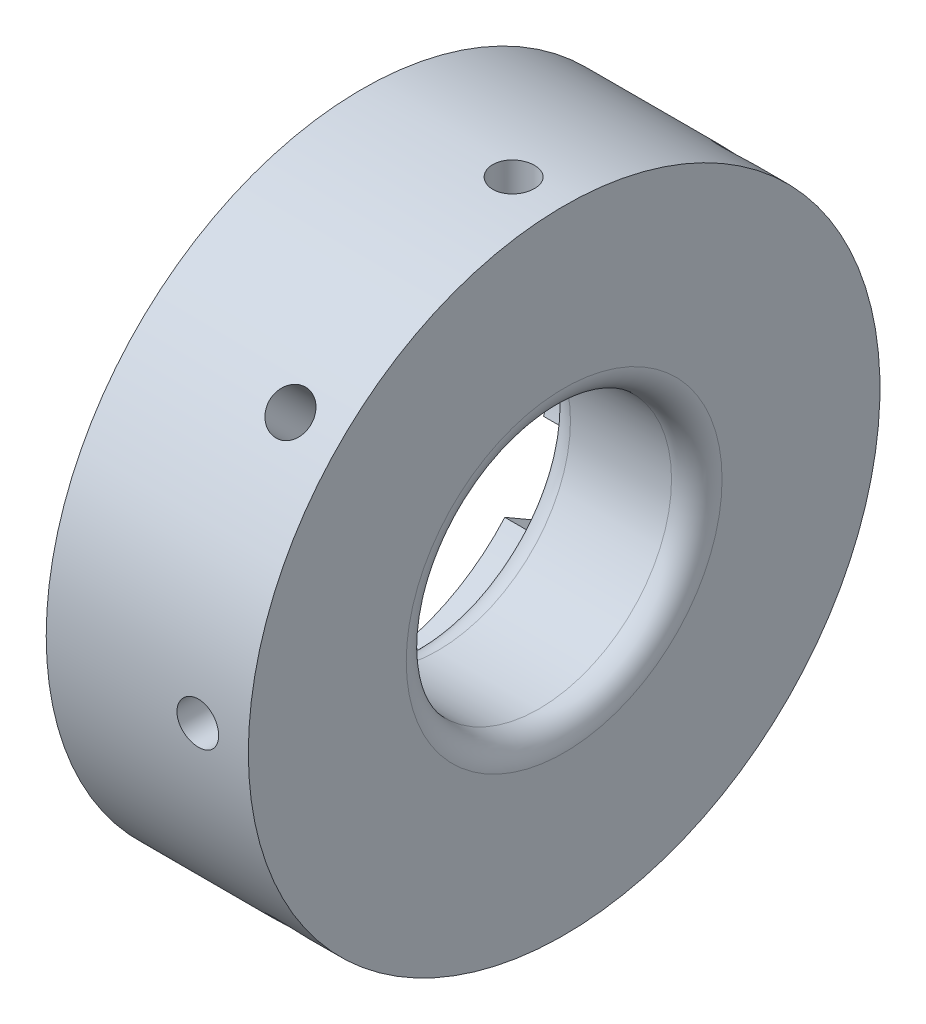
SolidWorks part; units mm, degrees
ref_plane "Plan de face" through (0, 0, 0) normal (0, 0, 1) x (1, 0, 0)
ref_plane "Plan de dessus" through (0, 0, 0) normal (0, 1, 0) x (1, 0, 0)
ref_plane "Plan de droite" through (0, 0, 0) normal (1, 0, 0) x (0, 0, -1)
sketch "Esquisse1" plane through (0, 0, 0) normal (0, 0, 1) x (1, 0, 0)
  line L0 (0, 0) -> (182.6544, 0) construction
  line L2 (0, 25) -> (16, 25)
  line L5 (16, 25) -> (16, 10.5)
  line L9 (0, 25) -> (0, 10.5)
  line L10 (0, 10.5) -> (16, 10.5)
  dimension "D1" = 25
  dimension "D2" = 21
  dimension "D4" = 16
revolve "Révolution1" add sketch "Esquisse1" angle 360 about L0
sketch "Esquisse2" plane through (0, 0, 0) normal (-1, 0, 0) x (0, 0, 1)
  line L0 (-3.02, 18.9998) -> (-3.02, 14.7949)
  line L1 (3.18, 18.9998) -> (3.18, 14.7614)
  line L2 (18.0443, 6.746) -> (14.3737, 4.6267)
  line L3 (14.9443, 12.1153) -> (11.3028, 10.0129)
  line L4 (14.8643, -12.2539) -> (11.1937, -10.1346)
  line L5 (17.9643, -6.8845) -> (14.3228, -4.7821)
  line L6 (-3.18, -18.9998) -> (-3.18, -14.7614)
  line L7 (3.02, -18.9998) -> (3.02, -14.7949)
  line L8 (-18.0443, -6.746) -> (-14.3737, -4.6267)
  line L9 (-14.9443, -12.1153) -> (-11.3028, -10.0129)
  line L10 (-14.8643, 12.2539) -> (-11.1937, 10.1346)
  line L11 (-17.9643, 6.8845) -> (-14.3228, 4.7821)
  circle A0 centre (0, 0) radius 15.1
  circle A1 centre (0, 0) radius 4.1
  circle A2 centre (0.08, 18.9998) radius 3.1
  circle A3 centre (16.4943, 9.4306) radius 3.1
  circle A4 centre (16.4143, -9.5692) radius 3.1
  circle A5 centre (-0.08, -18.9998) radius 3.1
  circle A6 centre (-16.4943, -9.4306) radius 3.1
  circle A7 centre (-16.4143, 9.5692) radius 3.1
  point P43 (0, 0)
  dimension "D1" = 8.2
  dimension "D2" = 30.2
  dimension "D3" = 6.2
  dimension "D6" = 6.2
  dimension "D4" = 19
  dimension "D5" = 6
extrude "Enlèv. mat.-Extru.1" cut sketch "Esquisse2" against normal blind 4 contours A0 A1 | A7 | A7 L11 A0 L10 | A6 | A6 L9 A0 L8 | A5 L7 A0 L6 | A4 L5 A0 L4 | A3 L3 A0 L2 | A3 | A4 | A2 | A2 L0 A0 L1
fillet "Congé2" radius 2 1 edges at (4, 0, 10.5)
fillet "Congé3" radius 2 1 edges at (16, 0, 10.5)
sketch "Esquisse3" plane through (0, 0, 0) normal (0, 0, 1) x (1, 0, 0)
  line L0 (0, 0) -> (16, 0) construction
  line L1 (16, -25) -> (16, 25) construction
  circle A0 centre (12, 0) radius 1.65
  dimension "D2" = 3.3
  dimension "D1" = 4
extrude "Enlèv. mat.-Extru.2" cut sketch "Esquisse3" against normal blind 10 from offset 25
pattern_circular "Répétition circulaire1" count 8 over 360 about axis through (0, 0, 0) along (1, 0, 0) of "Enlèv. mat.-Extru.2"
thread "Filetage1" pitch 0.7 start angle 0, offset 0, length 20, pitch 0.7, diameter 3.3
ref_plane "Plan1" through (13.65, -10.6066, -10.6066) normal (0, -0.7071, 0.7071) x (1, 0, 0)
sketch "Profil de filetage1" plane through (13.65, -10.6066, -10.6066) normal (0, -0.7071, 0.7071) x (1, 0, 0)
  line L0 (0, 0) -> (0, 0.7) construction
  line L1 (0, 0) -> (0.3789, 0.2187)
  line L2 (0.3789, 0.2187) -> (0.3789, 0.3062)
  line L3 (0.3789, 0.3062) -> (0, 0.525)
  line L4 (0.3789, 0.2625) -> (0, 0.2625) construction
  line L11 (0, 0) -> (0, 0.525)
  point P2 (0, 0)
  dimension "Pitch" = 0.7
  dimension "Profile_Angle" = 60
  dimension "Profile_Land" = 0.0875
  dimension "Profile_Height" = 0.3789
thread "Filetage2" pitch 0.7 start angle 0, offset 0, length 20, pitch 0.7, diameter 3.3
ref_plane "Plan2" through (13.65, 0, -15) normal (0, -1, 0) x (1, 0, 0)
sketch "Profil de filetage2" plane through (13.65, 0, -15) normal (0, -1, 0) x (1, 0, 0)
  line L0 (0, 0) -> (0, 0.7) construction
  line L1 (0, 0) -> (0.3789, 0.2187)
  line L2 (0.3789, 0.2187) -> (0.3789, 0.3062)
  line L3 (0.3789, 0.3062) -> (0, 0.525)
  line L4 (0.3789, 0.2625) -> (0, 0.2625) construction
  line L11 (0, 0) -> (0, 0.525)
  point P2 (0, 0)
  dimension "Pitch" = 0.7
  dimension "Profile_Angle" = 60
  dimension "Profile_Land" = 0.0875
  dimension "Profile_Height" = 0.3789
thread "Filetage3" pitch 0.7 start angle 0, offset 0, length 20, pitch 0.7, diameter 3.3
ref_plane "Plan3" through (10.35, 10.6066, -10.6066) normal (0, 0.7071, 0.7071) x (-1, 0, 0)
sketch "Profil de filetage3" plane through (10.35, 10.6066, -10.6066) normal (0, 0.7071, 0.7071) x (-1, 0, 0)
  line L0 (0, 0) -> (0, 0.7) construction
  line L1 (0, 0) -> (0.3789, 0.2187)
  line L2 (0.3789, 0.2187) -> (0.3789, 0.3062)
  line L3 (0.3789, 0.3062) -> (0, 0.525)
  line L4 (0.3789, 0.2625) -> (0, 0.2625) construction
  line L11 (0, 0) -> (0, 0.525)
  point P2 (0, 0)
  dimension "Pitch" = 0.7
  dimension "Profile_Angle" = 60
  dimension "Profile_Land" = 0.0875
  dimension "Profile_Height" = 0.3789
